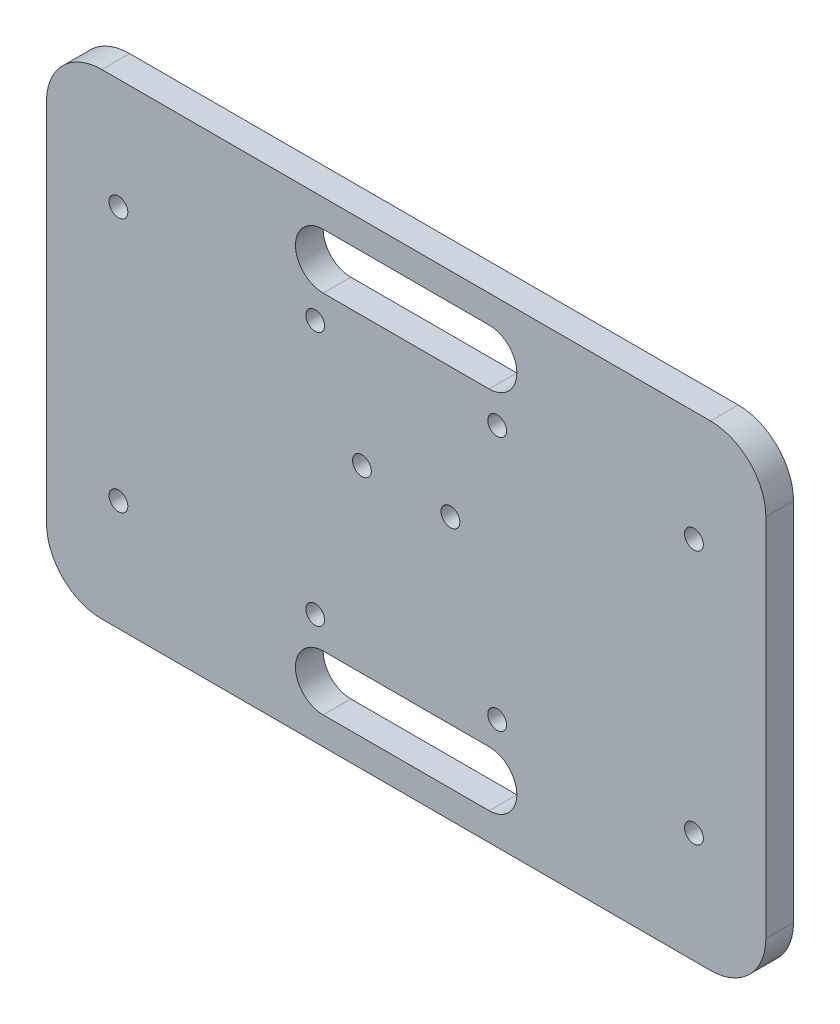
SolidWorks part; units mm, degrees
ref_plane "Front Plane" through (0, 0, 0) normal (0, 0, 1) x (1, 0, 0)
ref_plane "Top Plane" through (0, 0, 0) normal (0, 1, 0) x (1, 0, 0)
ref_plane "Right Plane" through (0, 0, 0) normal (1, 0, 0) x (0, 0, -1)
sketch "Sketch1" plane through (0, 0, 0) normal (0, 0, 1) x (1, 0, 0)
  line L0 (0, 43) -> (0, 33) construction
  line L1 (-55, 43) -> (55, 43)
  line L2 (-65, 33) -> (-65, -33)
  line L3 (-55, -43) -> (55, -43)
  line L4 (65, 33) -> (65, -33)
  line L5 (-65, 43) -> (65, -43) construction
  line L6 (-65, -43) -> (65, 43) construction
  line L7 (0, -43) -> (0, -33) construction
  line L8 (-15, 33) -> (15, 33) construction
  line L9 (-15, -33) -> (15, -33) construction
  line L10 (-15, 38) -> (15, 38)
  line L11 (-15, 28) -> (15, 28)
  line L12 (-52, -23) -> (-16.44, -23) construction
  line L13 (-15, -28) -> (15, -28)
  line L14 (-15, -38) -> (15, -38)
  line L15 (65, 43) -> (52, 43)
  line L16 (65, 43) -> (65, 23)
  line L17 (65, 23) -> (52, 23)
  line L18 (52, 43) -> (52, 23)
  line L19 (65, -43) -> (52, -43)
  line L20 (65, -43) -> (65, -23)
  line L21 (65, -23) -> (52, -23)
  line L22 (52, -43) -> (52, -23)
  line L23 (-65, -43) -> (-52, -43)
  line L24 (-65, -43) -> (-65, -23)
  line L25 (-65, -23) -> (-52, -23)
  line L26 (-52, -43) -> (-52, -23)
  line L27 (-65, 43) -> (-52, 43)
  line L28 (-65, 43) -> (-65, 23)
  line L29 (-65, 23) -> (-52, 23)
  line L30 (-52, 43) -> (-52, 23)
  line L45 (52, -23) -> (16.44, -23) construction
  line L46 (52, 23) -> (16.44, 23) construction
  arc A0 (-65, 33) -> (-55, 43) centre (-55, 33) cw
  arc A1 (65, 33) -> (55, 43) centre (55, 33) ccw
  arc A2 (55, -43) -> (65, -33) centre (55, -33) ccw
  arc A3 (-55, -43) -> (-65, -33) centre (-55, -33) cw
  arc A4 (-15, 38) -> (-15, 28) centre (-15, 33) ccw
  arc A5 (15, 28) -> (15, 38) centre (15, 33) ccw
  arc A6 (-15, -28) -> (-15, -38) centre (-15, -33) ccw
  arc A7 (15, -38) -> (15, -28) centre (15, -33) ccw
  circle A8 centre (52, 23) radius 1.7
  circle A9 centre (-52, 23) radius 1.7
  circle A10 centre (-52, -23) radius 1.7
  circle A11 centre (52, -23) radius 1.7
  circle A12 centre (8, 4.5) radius 1.7
  circle A13 centre (-8, 4.5) radius 1.7
  circle A14 centre (-16.44, -23) radius 1.7
  circle A15 centre (-16.44, 23) radius 1.7
  circle A16 centre (16.44, -23) radius 1.7
  circle A17 centre (16.44, 23) radius 1.7
  point P0 (0, 0)
  point P26 (0, 33)
  point P33 (0, -33)
  point P52 (0, 0)
  point P73 (0, 0)
  point P74 (7.4999, 4.5)
  point P75 (0, 0)
  dimension "D3" = 10
  dimension "D4" = 10
  dimension "D5" = 10
  dimension "D6" = 10
  dimension "D7" = 46
  dimension "D1" = 130
  dimension "D2" = 86
  dimension "D8" = 104
extrude "Boss-Extrude1" add sketch "Sketch1" along normal blind 5
